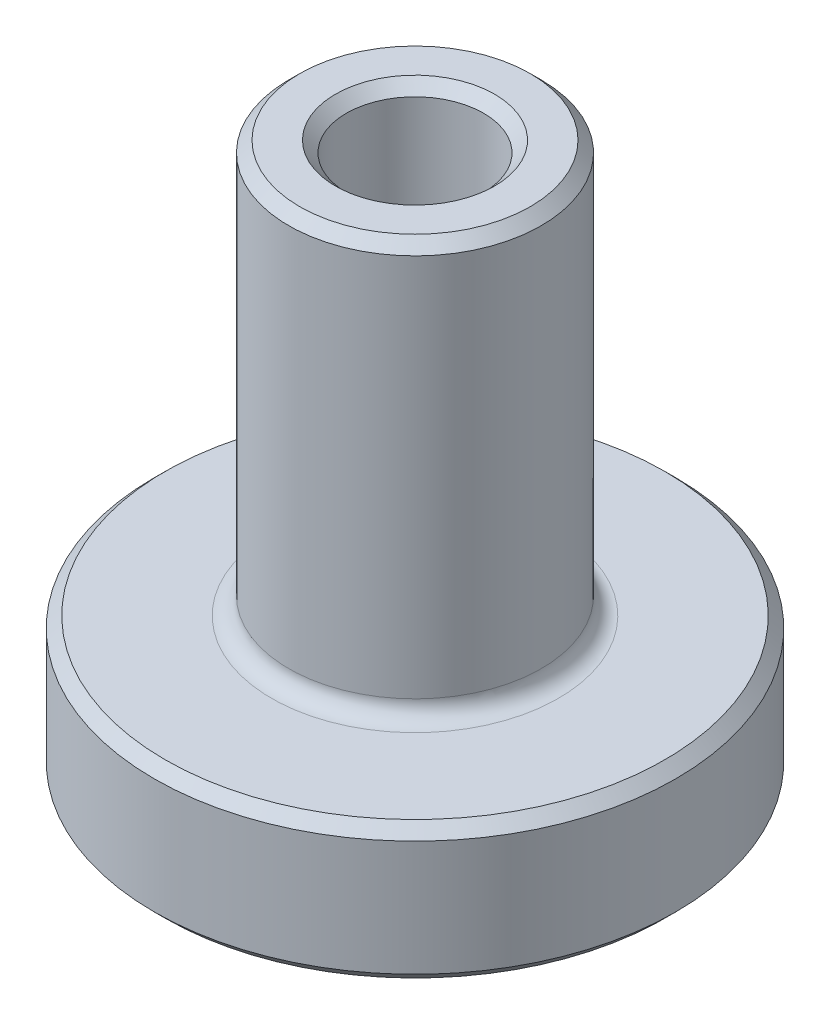
SolidWorks part; units mm, degrees
ref_plane "Front" through (0, 0, 0) normal (0, 0, 1) x (1, 0, 0)
ref_plane "Top" through (0, 0, 0) normal (0, 1, 0) x (1, 0, 0)
ref_plane "Right" through (0, 0, 0) normal (1, 0, 0) x (0, 0, -1)
sketch "Sketch1" plane through (0, 0, 0) normal (0, 0, 1) x (1, 0, 0)
  line L0 (0, 7.8865) -> (0, -7.8865) construction
  line L1 (1.5875, 0) -> (6.0325, 0)
  line L2 (6.0325, 0) -> (6.0325, 3.175)
  line L3 (6.0325, 3.175) -> (2.921, 3.175)
  line L4 (2.921, 3.175) -> (2.921, 12.7)
  line L5 (2.921, 12.7) -> (1.5875, 12.7)
  line L6 (1.5875, 12.7) -> (1.5875, 0)
  dimension "D1" = 3.175
  dimension "D2" = 3.175
  dimension "D3" = 5.842
  dimension "D4" = 9.525
  dimension "D5" = 12.065
revolve "Revolve1" add sketch "Sketch1" angle 360 about L0
fillet "Fillet1" radius 0.3969 1 edges at (0, 3.175, 2.921)
chamfer "Chamfer1" distance 0.254 angle 45 5 edges at (0, 0, 6.0325) (0, 3.175, 6.0325) (0, 12.7, 1.5875) (0, 0, 1.5875) (0, 12.7, 2.921)
